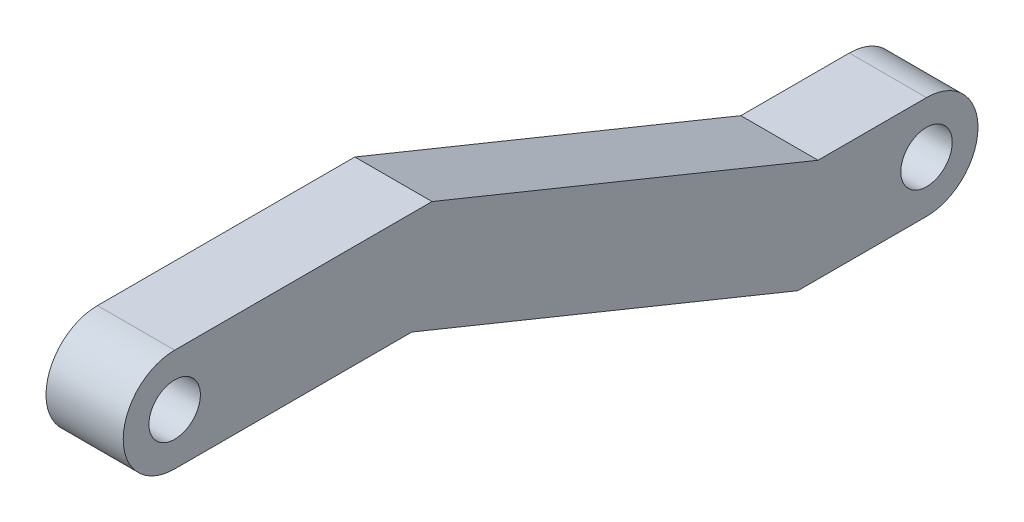
SolidWorks part; units mm, degrees
ref_plane "Front Plane" through (0, 0, 0) normal (0, 0, 1) x (1, 0, 0)
ref_plane "Top Plane" through (0, 0, 0) normal (0, 1, 0) x (1, 0, 0)
ref_plane "Right Plane" through (0, 0, 0) normal (1, 0, 0) x (0, 0, -1)
sketch "Sketch1" plane through (0, 0, 0) normal (1, 0, 0) x (0, 0, -1)
  line L4 (-16.09, -2) -> (16.09, -2)
  line L6 (-16.09, 2) -> (16.09, 2)
  line L8 (-16.09, -2) -> (16.09, 2) construction
  line L9 (-16.09, 2) -> (16.09, -2) construction
  arc A4 (16.09, 2) -> (16.09, -2) centre (16.09, 0) cw
  arc A5 (-16.09, 2) -> (-16.09, -2) centre (-16.09, 0) ccw
  circle A6 centre (-16.09, 0) radius 1
  circle A7 centre (16.09, 0) radius 1
  point P0 (0, 0)
  point P1 (0, 0)
  dimension "D2" = 4
  dimension "D3" = 2
  dimension "D1" = 32.18
sketch "Sketch2" plane through (0, 0, 0) normal (1, 0, 0) x (0, 0, -1)
  line L19 (-10.0015, -2) -> (19.2167, -8.1093) construction
  line L20 (15, -6.1093) -> (19.2167, -6.1093)
  line L21 (15, -6.1093) -> (0, 0)
  line L22 (0, 0) -> (-10.0015, 0)
  line L23 (14.2167, -10.1093) -> (19.2167, -10.1093)
  line L24 (14.2167, -10.1093) -> (-0.7833, -4)
  line L25 (-0.7833, -4) -> (-10.0015, -4)
  arc A6 (19.2167, -6.1093) -> (19.2167, -10.1093) centre (19.2167, -8.1093) cw
  arc A7 (-10.0015, 0) -> (-10.0015, -4) centre (-10.0015, -2) ccw
  circle A8 centre (-10.0015, -2) radius 1
  circle A9 centre (19.2167, -8.1093) radius 1
  dimension "D1" = 4
  dimension "D5" = 2
  dimension "D7" = 11.81
  dimension "D8" = 20
  dimension "D4" = 4
  dimension "D2" = 29.85
  dimension "D3" = 4
  dimension "D6" = 5
extrude "Boss-Extrude1" add sketch "Sketch2" along normal blind 3 contours L22
